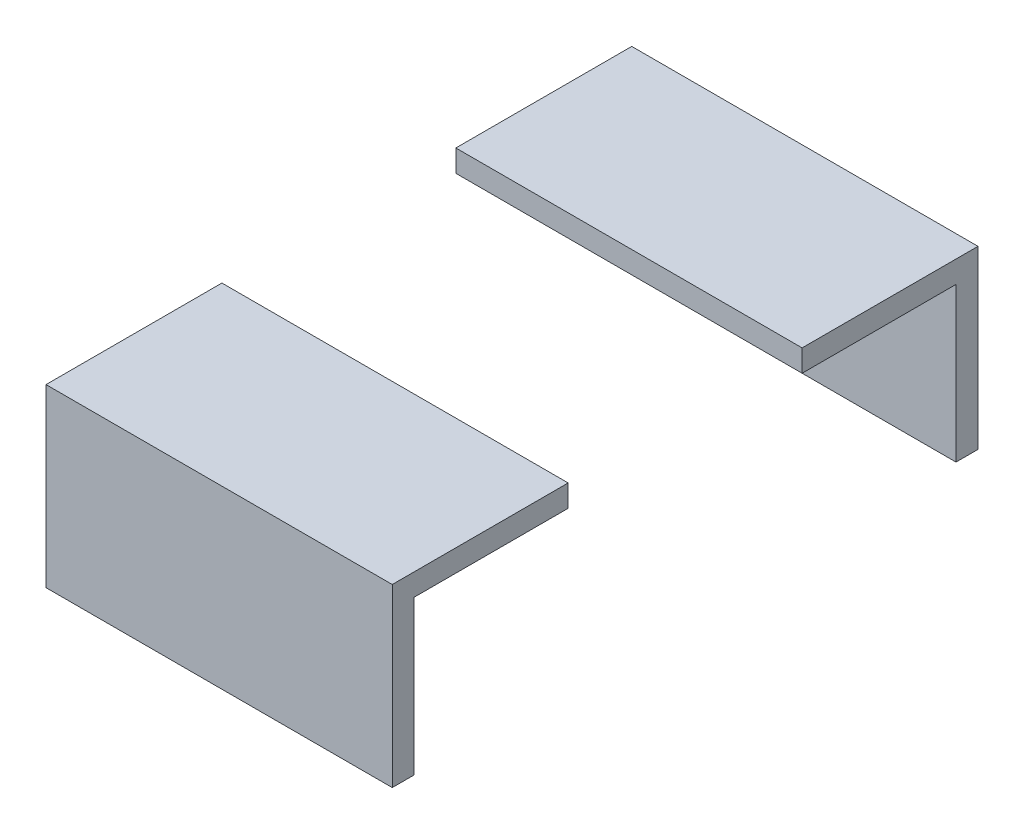
SolidWorks part; units mm, degrees
ref_plane "Front Plane" through (0, 0, 0) normal (0, 0, 1) x (1, 0, 0)
ref_plane "Top Plane" through (0, 0, 0) normal (0, 1, 0) x (1, 0, 0)
ref_plane "Right Plane" through (0, 0, 0) normal (1, 0, 0) x (0, 0, -1)
sketch "Sketch1" plane through (0, 0, 0) normal (1, 0, 0) x (0, 0, -1)
  line L0 (-15, 0) -> (15, 0) construction
  line L1 (15, 0) -> (18.5355, 3.5355) construction
  line L2 (-15, 0) -> (-18.5355, 3.5355) construction
  line L3 (0, 9.0451) -> (0, 0) construction
  point P4 (0, 0)
  dimension "D1" = 30
  dimension "D2" = 45
  dimension "D3" = 5
sketch "Sketch2" plane through (0, 0, 0) normal (1, 0, 0) x (0, 0, -1)
  line L0 (8.4455, 3.75) -> (19.558, 3.75)
  line L1 (19.558, 3.75) -> (19.558, -7.3625)
  line L2 (19.558, -7.3625) -> (21.1455, -7.3625)
  line L4 (8.4455, 3.75) -> (8.4455, 5.3375)
  line L5 (8.4455, 5.3375) -> (21.1455, 5.3375)
  line L6 (21.1455, 5.3375) -> (21.1455, -7.3625)
  line L8 (0, 9.0451) -> (0, 0) construction
  line L9 (0, 0) -> (0, -10.7325) construction
  line L10 (-21.1455, 5.3375) -> (-21.1455, -7.3625)
  line L11 (-8.4455, 5.3375) -> (-21.1455, 5.3375)
  line L12 (-8.4455, 3.75) -> (-8.4455, 5.3375)
  line L13 (-19.558, -7.3625) -> (-21.1455, -7.3625)
  line L14 (-19.558, 3.75) -> (-19.558, -7.3625)
  line L15 (-8.4455, 3.75) -> (-19.558, 3.75)
  dimension "D1" = 12.7
  dimension "D2" = 19.558
  dimension "D3" = 1.5875
  dimension "D4" = 3.75
extrude "Boss-Extrude1" add sketch "Sketch2" along normal mid plane 25
